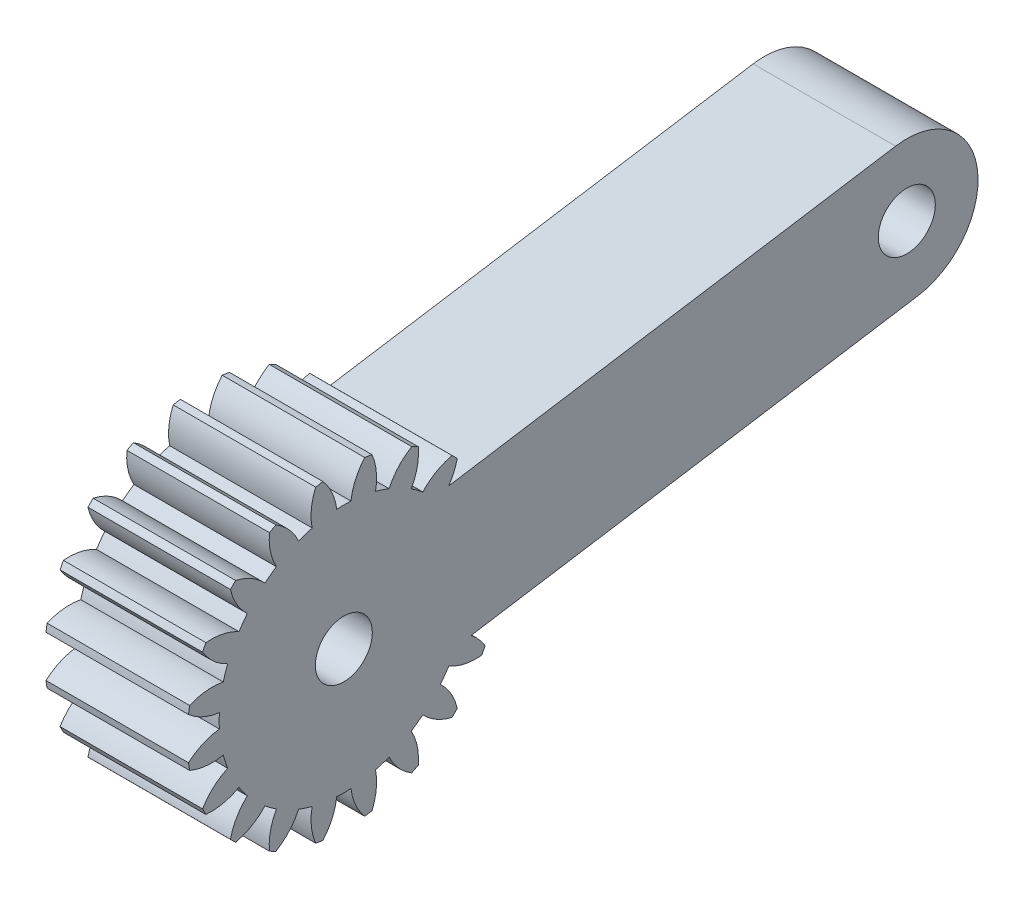
SolidWorks part; units mm, degrees
ref_plane "Plane1" through (0, 0, 0) normal (0, 0, 1) x (1, 0, 0)
ref_plane "Plane2" through (0, 0, 0) normal (0, 1, 0) x (1, 0, 0)
ref_plane "Plane3" through (0, 0, 0) normal (1, 0, 0) x (0, 0, -1)
sketch "HoldingSke" plane through (0, 0, 0) normal (0, 1, 0) x (1, 0, 0)
  line L0 (0, 0) -> (0.9397, -0.342)
  line L1 (-15, 0) -> (100, 0) construction
  line L2 (0, 0) -> (-2.1039, 2.3779)
  line L3 (0, 0) -> (-11.863, 4.5341)
  line L4 (0, 0) -> (8.1152, 2.9537)
  line L5 (0, 0) -> (-46.8476, -17.4728)
  line L6 (0, 0) -> (-8.2896, -5.593)
  line L7 (-2.1039, 2.3779) -> (8.6586, 51.2059)
  line L8 (-76.2, 54.61) -> (-76.1, 54.61)
  line L9 (-71.009, 38.7566) -> (-53.1078, 45.2721)
  line L10 (-76.2, 71.12) -> (104.1128, 71.12)
  line L11 (0, 0) -> (-10, 0)
  line L12 (-76.2, 101.6) -> (-76.162, 101.6)
  line L13 (24.9733, 27.94) -> (52.9518, 28.4284)
  line L14 (24.9733, 27.94) -> (24.9743, 27.94)
  line L15 (24.9733, 27.94) -> (100.4006, 29.5858)
  line L16 (-63.627, -1) -> (-12.827, -1)
  circle A0 centre (0, 0) radius 0.4
  circle A1 centre (0, 0) radius 8.749
  circle A2 centre (0, 0) radius 37.5
  circle A3 centre (0, 0) radius 0.4
  dimension "MHD" = 17.498
  dimension "Hub_dia" = 75
  dimension "Bore" = 0.8
  dimension "MBD" = 0.8
  dimension "Num_teeth" = 20
  dimension "Pitch" = 1
  dimension "Overall_len" = 50
  dimension "Show_teeth" = 20
  dimension "Thickness" = 10
  dimension "OAL" = 50.0001
  dimension "T_dim" = 0.1
  dimension "Ap" = 20
  dimension "H" = 19.05
  dimension "Pitch_radius" = 180.3128
  dimension "Width" = 10
  dimension "Backlash" = 0.038
  dimension "Addendum_fac" = 1
  dimension "Dedendum_fac" = 1.25
  dimension "Clearance_fac" = 0.25
  dimension "Dedendum_add" = 0.001
  dimension "Module" = 1
sketch "BasProSke" plane through (0, 0, 0) normal (0, 1, 0) x (1, 0, 0)
  line L0 (-10, 0) -> (60, 0) construction
  line L1 (0, 0) -> (0, 11)
  line L2 (0, 0) -> (10, 0)
  line L3 (10, 0) -> (10, 11)
  line L4 (10, 11) -> (0, 11)
  dimension "Thickness" = 10
  dimension "Diameter" = 22
revolve "Base-Revolve" add sketch "BasProSke" angle 360 about L0
sketch "TooCutSke" plane through (0, 0, 0) normal (1, 0, 0) x (0, 0, -1)
  line L1 (0, 0) -> (0, 107) construction
  line L2 (0, 0) -> (-0.8511, 9.9637) construction
  line L3 (0, 0) -> (-3.1206, 19.7028) construction
  line L4 (-0.8511, 9.9637) -> (-1.5603, 9.8514) construction
  arc A0 (0.4999, 8.7347) -> (-0.4999, 8.7347) centre (0, 0) ccw
  arc A1 (1.4852, 10.9249) -> (-1.4852, 10.9249) centre (0, 0) ccw
  circle A2 centre (0, 0) radius 10 construction
  circle A3 centre (0, 0) radius 9.3969 construction
  arc A4 (-0.4999, 8.7347) -> (-1.4852, 10.9249) centre (-4.4722, 8.2645) ccw
  arc A5 (1.4852, 10.9249) -> (0.4999, 8.7347) centre (4.4722, 8.2645) ccw
  dimension "Root_dia" = 17.498
  dimension "Overcut_dia" = 22.0508
  dimension "Pitch_dia" = 20
  dimension "Base_dia" = 18.7939
  dimension "Flank_rad" = 4
  dimension "Half_ang" = 9
  dimension "Half_CT" = 0.7181
extrude "ToothCut" cut sketch "TooCutSke" along normal through all
fillet "Breaks" [suppressed] radius 0.02
fillet "RootFillets" [suppressed] radius 0.251
pattern_circular "TeethCuts" count 20 every 18 about axis through (-10, 0, 0) along (1, 0, 0) of "ToothCut", "RootFillets", "Breaks"
sketch "HubNeaOneSke" plane through (0, 0, 0) normal (-1, 0, 0) x (0, 0, 1)
  circle A0 centre (0, 0) radius 8.749
  dimension "Diameter" = 17.498
extrude "HubNearOne" [suppressed] add sketch "HubNeaOneSke" along normal blind 40.0001
sketch "HubNeaBotSke" plane through (0, 0, 0) normal (-1, 0, 0) x (0, 0, 1)
  circle A0 centre (0, 0) radius 8.749
  dimension "Diameter" = 17.498
extrude "HubNearBoth" [suppressed] add sketch "HubNeaBotSke" along normal blind 20
ref_plane "FarPln" through (10, 0, 0) normal (1, 0, 0) x (0, 0, -1)
sketch "HubFarSke" plane through (10, 0, 0) normal (1, 0, 0) x (0, 0, -1)
  circle A0 centre (0, 0) radius 8.749
  dimension "Diameter" = 17.498
extrude "HubFar" [suppressed] add sketch "HubFarSke" along normal blind 20
sketch "BorSke" plane through (0, 0, 0) normal (1, 0, 0) x (0, 0, -1)
  circle A0 centre (0, 0) radius 0.4
  dimension "Diameter" = 0.8
extrude "Bore" cut sketch "BorSke" along normal mid plane 100.0001
sketch "KeySke" plane through (0, 0, 0) normal (1, 0, 0) x (0, 0, -1)
  line L0 (-0.05, 0) -> (-0.05, 0.5)
  line L1 (-0.05, 0.5) -> (0.05, 0.5)
  line L2 (0.05, 0.5) -> (0.05, 0)
  line L3 (0, 0) -> (0, 34) construction
  line L4 (-0.05, 0) -> (0.05, 0)
  dimension "Offset" = 0.5
  dimension "Width" = 0.1
extrude "Keyway" [suppressed] cut sketch "KeySke" along normal mid plane 100.0001
pattern_circular "Keyway2" [suppressed] count 2 every 90 about axis through (-10, 0, 0) along (1, 0, 0)
sketch "Croquis1" plane through (10, 0, 0) normal (1, 0, 0) x (0, 0, -1)
  line L0 (0, 0) -> (39.5075, 6.2574) construction
  line L1 (38.7254, 11.1958) -> (-0.7822, 4.9384)
  line L2 (40.2897, 1.3189) -> (0.7822, -4.9384)
  arc A0 (-0.7822, 4.9384) -> (0.7822, -4.9384) centre (0, 0) ccw
  circle A1 centre (0, 0) radius 2
  circle A2 centre (39.5075, 6.2574) radius 2
  arc A3 (40.2897, 1.3189) -> (38.7254, 11.1958) centre (39.5075, 6.2574) ccw
extrude "Saliente-Extruir1" add sketch "Croquis1" against normal blind 10
sketch "Croquis2" plane through (10, 0, 0) normal (1, 0, 0) x (0, 0, -1)
  circle A0 centre (0, 0) radius 2
extrude "Cortar-Extruir1" cut sketch "Croquis2" against normal blind 10
equation "' \"Module@HoldingSke\" = 6.35"
equation "' \"Num_teeth@HoldingSke\" = 12"
equation "' \"Ap@HoldingSke\" =  20"
equation "' \"Ap@HoldingSke\" = 20"
equation "' \"Width@HoldingSke\" = 0.5 * 25.4"
equation "' \"Hub_dia@HoldingSke\"= 1 * 25.4"
equation "' \"Hub_dia@HoldingSke\" = 1 * 25.4"
equation "' \"Overall_len@HoldingSke\" = 1.0 * 25.4"
equation "' \"Bore@HoldingSke\" = 0.75 * 25.4"
equation "' \"T_dim@HoldingSke\" = 0.1 * 25.4"
equation "' \"Width@KeySke\" = 0.25 * 25.4"
equation "' \"Show_teeth@HoldingSke\" = 13"
equation "' \"Backlash@HoldingSke\" = 0.009 * 25.4"
equation "' \"Addendum_fac@HoldingSke\" = 1.0"
equation "' \"Dedendum_fac@HoldingSke\" = 1.25"
equation "' \"Dedendum_add@HoldingSke\" = 0.00005 * 25.4"
equation "' \"Clearance_fac@HoldingSke\" = 0.25"
equation "\"Pitch@HoldingSke\" = 1 / \"Module@HoldingSke\""
equation "\"Overcut_dia@TooCutSke\" = (\"Num_teeth@HoldingSke\" + 2 * \"Addendum_fac@HoldingSke\") / \"Pitch@HoldingSke\" + 0.002 * 25.4"
equation "\"Pitch_dia@TooCutSke\" = \"Num_teeth@HoldingSke\" / \"Pitch@HoldingSke\""
equation "\"Base_dia@TooCutSke\" = \"Num_teeth@HoldingSke\" / \"Pitch@HoldingSke\" * cos((\"Ap@HoldingSke\"  * 3.14159265 / 180))"
equation "\"Root_dia@TooCutSke\" = (\"Num_teeth@HoldingSke\" + 2) / \"Pitch@HoldingSke\" - 2 * (\"Addendum_fac@HoldingSke\" + \"Dedendum_fac@HoldingSke\") / \"Pitch@HoldingSke\" - \"Dedendum_add@HoldingSke\" * 2"
equation "\"Half_ang@TooCutSke\" = 180 / \"Num_teeth@HoldingSke\""
equation "\"Half_CT@TooCutSke\" = \"Num_teeth@HoldingSke\" / \"Pitch@HoldingSke\" * sin((3.14159265 / 2 / \"Num_teeth@HoldingSke\")) / 2 - 7 * \"Backlash@HoldingSke\" / 4"
equation "\"Flank_rad@TooCutSke\" = \"Num_teeth@HoldingSke\" / \"Pitch@HoldingSke\" / 5"
equation "\"Radius@RootFillets\" = \"Clearance_fac@HoldingSke\" / \"Pitch@HoldingSke\" + \"Dedendum_add@HoldingSke\""
equation "\"Break_rad@Breaks\" = 0.02 / \"Pitch@HoldingSke\""
equation "\"Thickness@HoldingSke\" = \"Width@HoldingSke\""
equation "\"OAL@HoldingSke\" = \"Thickness@HoldingSke\""
equation "\"MHD@HoldingSke\" = (\"Num_teeth@HoldingSke\" + 2) / \"Pitch@HoldingSke\" - 2 * (\"Addendum_fac@HoldingSke\" + \"Dedendum_fac@HoldingSke\")  / \"Pitch@HoldingSke\" - \"Dedendum_add@HoldingSke\" * 2"
equation "\"MBD@HoldingSke\" = (\"Num_teeth@HoldingSke\" + 2) / \"Pitch@HoldingSke\" - 2 * (\"Addendum_fac@HoldingSke\" + \"Dedendum_fac@HoldingSke\")  / \"Pitch@HoldingSke\" - \"Dedendum_add@HoldingSke\" * 2 - 0.002 * 25.4"
equation "\"MHD@HoldingSke\" = ((sgn( \"MHD@HoldingSke\" - \"Hub_dia@HoldingSke\" )-1)*( \"MHD@HoldingSke\" - \"Hub_dia@HoldingSke\" ))/-2+ \"Hub_dia@HoldingSke\""
equation "\"MBD@HoldingSke\" = ((sgn( \"MBD@HoldingSke\" - \"Bore@HoldingSke\" )-1)*( \"MBD@HoldingSke\" - \"Bore@HoldingSke\" ))/-2+ \"Bore@HoldingSke\""
equation "\"OAL@HoldingSke\" = ((sgn( \"OAL@HoldingSke\" - \"Overall_len@HoldingSke\" )+1)*( \"OAL@HoldingSke\" - \"Overall_len@HoldingSke\" ))/2 + \"Overall_len@HoldingSke\" + 0.000002 * 25.4"
equation "\"Num_teeth@TeethCuts\" = int( \"Show_teeth@HoldingSke\" ) + 1"
equation "\"Num_teeth@TeethCuts\" = ((sgn( \"Num_teeth@TeethCuts\" - \"Num_teeth@HoldingSke\" )-1)*( \"Num_teeth@TeethCuts\" - \"Num_teeth@HoldingSke\" ))/-2+ \"Num_teeth@HoldingSke\""
equation "\"Num_teeth@TeethCuts\" = ((sgn( \"Num_teeth@TeethCuts\" - 2.0)+1)*( \"Num_teeth@TeethCuts\" - 2.0))/2 +2.0"
equation "\"Angle@TeethCuts\" = 360.0 / \"Num_teeth@HoldingSke\""
equation "\"Diameter@BasProSke\" = (\"Num_teeth@HoldingSke\" + 2 * \"Addendum_fac@HoldingSke\") / \"Pitch@HoldingSke\""
equation "\"Thickness@BasProSke\"  = \"Thickness@HoldingSke\""
equation "' \"Fillet_rad@BasProSke\" =  \"Thickness@HoldingSke\" * 0.05"
equation "' \"Fillet_rad@BasProSke\" = \"Thickness@HoldingSke\" * 0.05"
equation "\"MHD@HoldingSke\" = ((sgn( \"MHD@HoldingSke\" - \"Root_dia@TooCutSke\" )-1)*( \"MHD@HoldingSke\" - \"Root_dia@TooCutSke\" ))/-2+ \"Root_dia@TooCutSke\""
equation "\"Diameter@HubNeaOneSke\" = \"MHD@HoldingSke\""
equation "\"Length@HubNearOne\" = \"OAL@HoldingSke\" - \"Thickness@BasProSke\""
equation "\"Diameter@HubNeaBotSke\" = \"MHD@HoldingSke\""
equation "\"Length@HubNearBoth\" = ( \"OAL@HoldingSke\" - \"Thickness@BasProSke\" ) / 2.0"
equation "\"Thickness@FarPln\" = \"Thickness@BasProSke\""
equation "\"Diameter@HubFarSke\" = \"MHD@HoldingSke\""
equation "\"Length@HubFar\" = ( \"OAL@HoldingSke\" - \"Thickness@BasProSke\" ) / 2.0"
equation "\"Diameter@BorSke\" = \"MBD@HoldingSke\""
equation "\"D1@Bore\" = \"OAL@HoldingSke\" * 2.0"
equation "\"D1@Keyway\" = \"OAL@HoldingSke\" * 2.0"
equation "\"Offset@KeySke\" = \"T_dim@HoldingSke\" + \"MBD@HoldingSke\" / 2.0"
